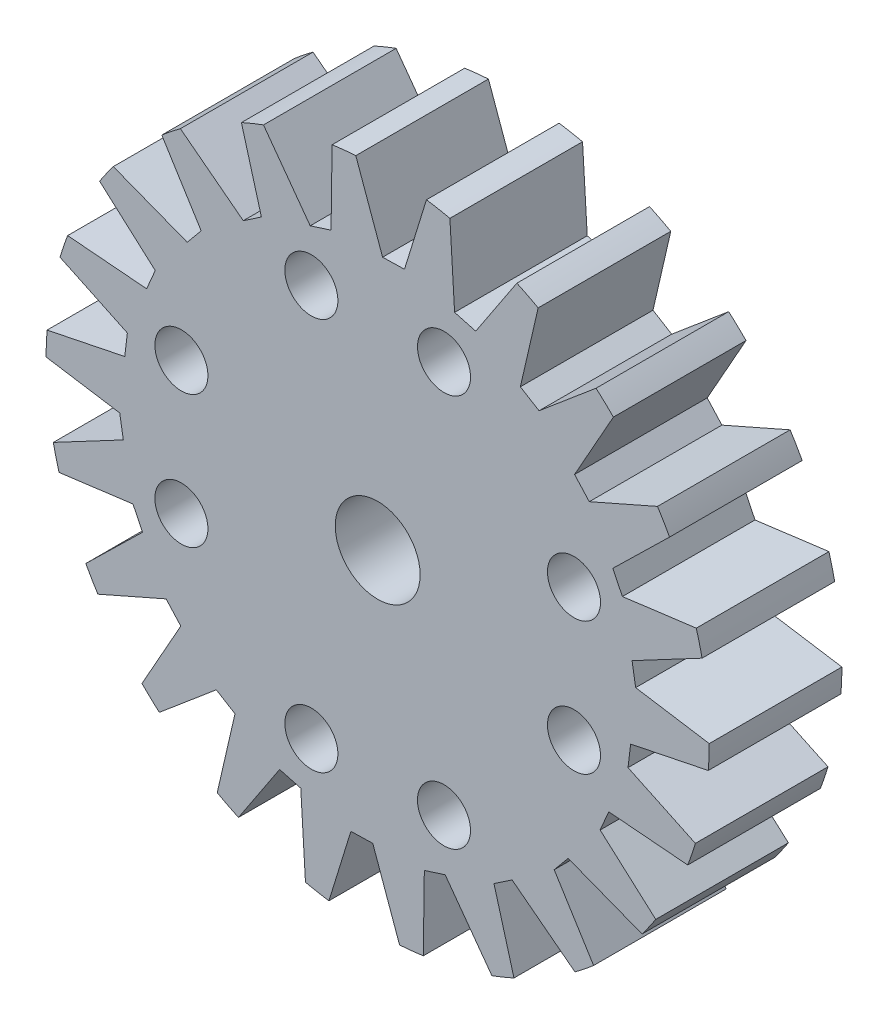
SolidWorks part; units mm, degrees
other "Markup1"
sketch "Sketch3" plane through (-11.5, 11.4999, 3) normal (-0.0441, 0.0247, 0.9987) x (0.9973, -0.0583, 0.0455)
ref_plane "Front Plane" through (0, 0, 0) normal (0, 0, 1) x (1, 0, 0)
ref_plane "Top Plane" through (0, 0, 0) normal (0, 1, 0) x (1, 0, 0)
ref_plane "Right Plane" through (0, 0, 0) normal (1, 0, 0) x (0, 0, -1)
sketch "Sketch1" plane through (0, 0, 0) normal (0, 0, 1) x (1, 0, 0)
  line L2 (-2.5, 7.4) -> (2.5, 7.4) construction
  line L3 (-2.5, -7.4) -> (2.5, -7.4) construction
  line L4 (-7.4, -2.5) -> (-7.4, 2.5) construction
  line L5 (7.4, -2.5) -> (7.4, 2.5) construction
  circle A0 centre (0, 0) radius 12.5
  circle A1 centre (0, 0) radius 10.5 construction
  circle A2 centre (0, 0) radius 1.6
  circle A3 centre (-2.5, 7.4) radius 1
  circle A5 centre (2.5, 7.4) radius 1
  circle A6 centre (2.5, -7.4) radius 1
  circle A8 centre (-2.5, -7.4) radius 1
  circle A9 centre (7.4, -2.5) radius 1
  circle A11 centre (7.4, 2.5) radius 1
  circle A12 centre (-7.4, 2.5) radius 1
  circle A14 centre (-7.4, -2.5) radius 1
  dimension "D1" = 25
  dimension "D2" = 21
  dimension "3,2" = 3.2
  dimension "D4" = 2
  dimension "D6" = 2
  dimension "D10" = 2
  dimension "D12" = 2
extrude "Boss-Extrude1" add sketch "Sketch1" along normal blind 5
sketch "Sketch2" plane through (0, 0, 5) normal (0, 0, 1) x (1, 0, 0)
  line L0 (-5.1888, 11.5792) -> (-7.4471, 10.0542)
  line L1 (-7.4471, 10.0542) -> (-5.0673, 8.2276)
  line L2 (-5.0673, 8.2276) -> (-4.3836, 8.6893)
  line L3 (-4.3836, 8.6893) -> (-5.1888, 11.5792)
  line L4 (-5.0673, 8.2276) -> (-7.6364, 6.4928) construction
  line L5 (-7.6364, 6.4928) -> (-8.4416, 9.3827) construction
  line L6 (-8.4416, 9.3827) -> (-7.4471, 10.0542) construction
  circle A0 centre (0, 0) radius 11.2076 construction
  circle A1 centre (0, 0) radius 12.5 construction
  point P11 (-4.7862, 10.1343)
  point P12 (-6.2572, 9.1409)
  dimension "D1" = 2.725
  dimension "D2" = 0.825
  dimension "D4" = 3
  dimension "D5" = 3.1
  dimension "D6" = 1.2
extrude "Cut-Extrude1" cut sketch "Sketch2" against normal through all
pattern_circular "CirPattern1" count 22 over 360 about axis through (0, 0, 0) along (0, 0, 1) of "Cut-Extrude1"
